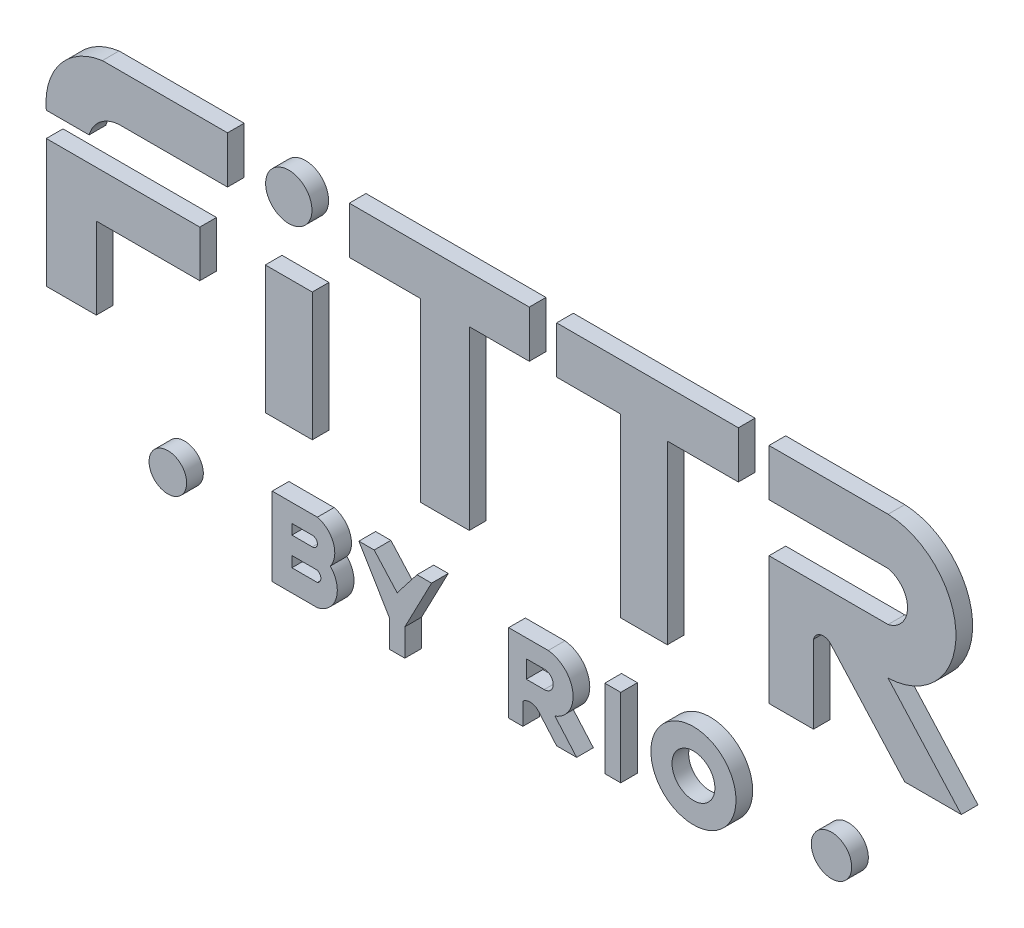
SolidWorks part; units mm, degrees
ref_plane "Front Plane" through (0, 0, 0) normal (0, 0, 1) x (1, 0, 0)
ref_plane "Top Plane" through (0, 0, 0) normal (0, 1, 0) x (1, 0, 0)
ref_plane "Right Plane" through (0, 0, 0) normal (1, 0, 0) x (0, 0, -1)
sketch "Sketch1" plane through (0, 0, 0) normal (0, 0, 1) x (1, 0, 0)
  line L0 (-272.3284, 1988.7665) -> (-272.3284, 1912.0744)
  line L1 (-272.3284, 1912.0744) -> (-242.3706, 1912.0744)
  line L2 (-242.3706, 1912.0744) -> (-242.3706, 1960.9057)
  line L3 (-242.3706, 1960.9057) -> (-180.3579, 1960.9057)
  line L4 (-180.3579, 1960.9057) -> (-180.3579, 1988.7665)
  line L5 (-180.3579, 1988.7665) -> (-272.3284, 1988.7665)
  line L6 (-141.1131, 1988.7665) -> (-141.1131, 1912.0744)
  line L7 (-141.1131, 1912.0744) -> (-112.9528, 1912.0744)
  line L8 (-112.9528, 1912.0744) -> (-112.9528, 1988.7665)
  line L9 (-112.9528, 1988.7665) -> (-141.1131, 1988.7665)
  line L10 (-48.2439, 2017.8255) -> (-48.2439, 1912.0744)
  line L11 (-48.2439, 1912.0744) -> (-18.8852, 1912.0744)
  line L12 (-18.8852, 1912.0744) -> (-18.8852, 2017.8255)
  line L13 (-18.8852, 2017.8255) -> (17.0642, 2017.8255)
  line L14 (17.0642, 2017.8255) -> (17.0642, 2045.9859)
  line L15 (17.0642, 2045.9859) -> (-90.784, 2045.9859)
  line L16 (-90.784, 2045.9859) -> (-90.784, 2017.8255)
  line L17 (-90.784, 2017.8255) -> (-48.2439, 2017.8255)
  line L18 (71.8777, 2017.8255) -> (71.8777, 1912.0744)
  line L19 (71.8777, 1912.0744) -> (99.773, 1912.0744)
  line L20 (99.773, 1912.0744) -> (99.773, 2017.8255)
  line L21 (99.773, 2017.8255) -> (142.35, 2017.8255)
  line L22 (142.35, 2017.8255) -> (142.35, 2045.9859)
  line L23 (142.35, 2045.9859) -> (33.4606, 2045.9859)
  line L24 (33.4606, 2045.9859) -> (33.4606, 2017.8255)
  line L25 (33.4606, 2017.8255) -> (71.8777, 2017.8255)
  line L26 (160.7022, 1988.7665) -> (160.7022, 1912.0744)
  line L27 (160.7022, 1912.0744) -> (187.3739, 1912.0744)
  line L28 (187.3739, 1912.0744) -> (187.3739, 1958.7508)
  line L29 (198.1476, 1960.9057) -> (242.0166, 1912.0744)
  line L30 (242.0166, 1912.0744) -> (275.9419, 1912.0744)
  line L31 (275.9419, 1912.0744) -> (232.0729, 1960.9057)
  line L32 (160.7022, 1988.7665) -> (232.0729, 1988.7665)
  line L33 (160.7022, 2045.9859) -> (160.7022, 2017.8255)
  line L34 (160.7022, 2017.8255) -> (232.0729, 2017.8255)
  line L35 (160.7022, 2045.9859) -> (232.0729, 2045.9859)
  line L36 (-272.3284, 2003.4296) -> (-246.6703, 2003.4296)
  line L37 (-226.9126, 2017.8255) -> (-163.753, 2017.8255)
  line L38 (-163.753, 2017.8255) -> (-163.753, 2045.9859)
  line L39 (-163.753, 2045.9859) -> (-226.9126, 2045.9859)
  line L40 (-226.9126, 2045.9859) -> (-238.7348, 2045.9859)
  line L41 (-136.9779, 1873.4631) -> (-136.9779, 1826.4801)
  line L42 (-136.9779, 1826.4801) -> (-109.9029, 1826.4801)
  line L43 (-136.9779, 1873.4631) -> (-109.9029, 1873.4631)
  line L44 (-125.1753, 1862.599) -> (-125.1753, 1856.5312)
  line L45 (-125.1753, 1856.5312) -> (-112.9528, 1856.5312)
  line L46 (-125.1753, 1862.599) -> (-112.9528, 1862.599)
  line L47 (-125.1753, 1845.9513) -> (-125.1753, 1839.5724)
  line L48 (-125.1753, 1839.5724) -> (-112.9528, 1839.5724)
  line L49 (-125.1753, 1845.9513) -> (-112.9528, 1845.9513)
  line L50 (-112.9528, 1845.9513) -> (-109.9029, 1845.9513)
  line L51 (-112.9528, 1839.5724) -> (-109.9029, 1839.5724)
  line L52 (-85.0343, 1873.4631) -> (-66.6752, 1842.7619)
  line L53 (-66.6752, 1842.7619) -> (-66.6752, 1826.4801)
  line L54 (-66.6752, 1826.4801) -> (-57.4956, 1826.4801)
  line L55 (-57.4956, 1826.4801) -> (-57.4956, 1842.7619)
  line L56 (-57.4956, 1842.7619) -> (-41.4704, 1873.4631)
  line L57 (-41.4704, 1873.4631) -> (-50.1843, 1873.4631)
  line L58 (-50.1843, 1873.4631) -> (-62.0854, 1858.1125)
  line L59 (-62.0854, 1858.1125) -> (-75.8547, 1873.4631)
  line L60 (-75.8547, 1873.4631) -> (-85.0343, 1873.4631)
  line L61 (4.7086, 1873.4631) -> (4.7086, 1826.4801)
  line L62 (4.7086, 1826.4801) -> (13.2284, 1826.4801)
  line L63 (13.2284, 1826.4801) -> (13.2284, 1839.5724)
  line L64 (4.7086, 1873.4631) -> (28.4157, 1873.4631)
  line L65 (15.2657, 1862.599) -> (15.2657, 1851.9624)
  line L66 (15.2657, 1851.9624) -> (26.008, 1851.9624)
  line L67 (15.2657, 1862.599) -> (26.008, 1862.599)
  line L68 (22.0959, 1839.5724) -> (33.4606, 1826.4801)
  line L69 (33.4606, 1826.4801) -> (45.4406, 1826.4801)
  line L70 (45.4406, 1826.4801) -> (32.4677, 1841.4251)
  line L71 (62.3238, 1873.4631) -> (62.3238, 1826.4801)
  line L72 (62.3238, 1826.4801) -> (71.8777, 1826.4801)
  line L73 (71.8777, 1826.4801) -> (71.8777, 1873.4631)
  line L74 (71.8777, 1873.4631) -> (62.3238, 1873.4631)
  circle A0 centre (-127.033, 2031.1227) radius 13.873
  circle A1 centre (-199.4893, 1851.9624) radius 11.2617
  circle A2 centre (198.1476, 1851.9624) radius 12.096
  arc A3 (232.0729, 2017.8255) -> (232.0729, 1988.7665) centre (228.8278, 2003.296) cw
  arc A4 (232.0729, 2045.9859) -> (232.0729, 1960.9057) centre (230.1472, 2003.4458) cw
  arc A5 (-272.3284, 2003.4296) -> (-238.7348, 2045.9859) centre (-233.4063, 2007.2423) cw
  arc A6 (-246.6703, 2003.4296) -> (-226.9126, 2017.8255) centre (-227.5737, 1997.9766) cw
  arc A7 (-109.9029, 1873.4631) -> (-102.1486, 1851.9624) centre (-113.2015, 1860.1248) cw
  arc A8 (-109.9029, 1826.4801) -> (-102.1486, 1851.9624) centre (-113.2682, 1841.4251) ccw
  arc A9 (-112.9528, 1862.599) -> (-112.9528, 1856.5312) centre (-112.8849, 1859.5651) cw
  arc A10 (-109.9029, 1845.9513) -> (-109.9029, 1839.5724) centre (-111.2845, 1842.7619) cw
  arc A11 (26.008, 1862.599) -> (26.008, 1851.9624) centre (26.0805, 1857.2807) cw
  arc A12 (28.4157, 1873.4631) -> (32.4677, 1841.4251) centre (26.7494, 1856.9771) cw
  arc A13 (13.2284, 1839.5724) -> (22.0959, 1839.5724) centre (17.6621, 1834.6146) cw
  circle A14 centre (115.4352, 1851.9624) radius 12.8515
  circle A15 centre (115.4352, 1851.9624) radius 25.4976
  arc A16 (187.3739, 1958.7508) -> (198.1476, 1960.9057) centre (193.2488, 1957.3882) cw
extrude "Boss-Extrude1" add sketch "Sketch1" along normal blind 10
